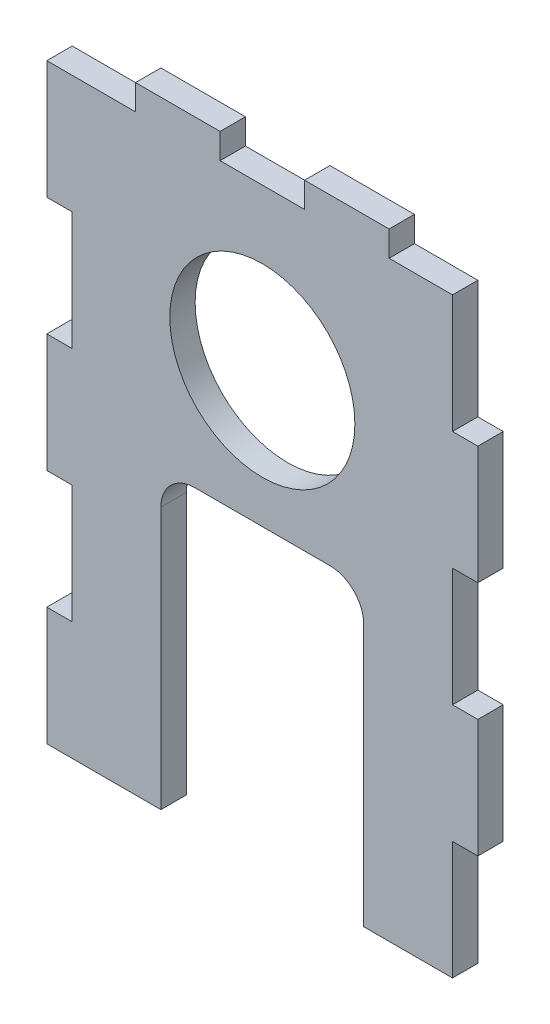
SolidWorks part; units mm, degrees
material "PC High Viscosity"
ref_plane "Front Plane" through (0, 0, 0) normal (0, 0, 1) x (1, 0, 0)
ref_plane "Top Plane" through (0, 0, 0) normal (0, 1, 0) x (1, 0, 0)
ref_plane "Right Plane" through (0, 0, 0) normal (1, 0, 0) x (0, 0, -1)
sketch "Sketch1" plane through (0, 0, 0) normal (0, 0, 1) x (1, 0, 0)
  line L1 (-22.5, -35) -> (22.5, -35)
  line L2 (-22.5, -35) -> (-22.5, 35)
  line L3 (-22.5, 35) -> (22.5, 35)
  line L4 (22.5, -35) -> (22.5, 35)
  line L5 (-22.5, -35) -> (22.5, 35) construction
  line L6 (-22.5, 35) -> (22.5, -35) construction
  point P0 (0, 0)
  dimension "D1" = 70
  dimension "D2" = 45
extrude "Boss-Extrude1" add sketch "Sketch1" along normal blind 3 contours L2 L3 L4 L1
sketch "Sketch2" plane through (0, 0, 3) normal (0, 0, 1) x (1, 0, 0)
  line L0 (-22.5, -35) -> (22.5, -35) construction
  line L1 (-12, 0) -> (12, 0)
  line L2 (-12, 0) -> (-12, -35)
  line L3 (-12, -35) -> (12, -35)
  line L4 (12, 0) -> (12, -35)
  line L5 (-12, 0) -> (12, -35) construction
  line L6 (-12, -35) -> (12, 0) construction
  circle A0 centre (0, 16) radius 10.95
  point P2 (0, -17.5)
  dimension "D1" = 21.9
  dimension "D2" = 16
  dimension "D3" = 24
  dimension "D4" = 35
extrude "Cut-Extrude1" cut sketch "Sketch2" against normal through all
fillet "Fillet1" radius 4 2 edges at (12, 0, 1.5) (-12, 0, 1.5)
sketch "Sketch4" plane through (0, 0, 3) normal (0, 0, 1) x (1, 0, 0)
  line L0 (0, 35) -> (0, 41.52) construction
  line L1 (-15, 35) -> (-5, 35)
  line L2 (-15, 35) -> (-15, 38)
  line L3 (-15, 38) -> (-5, 38)
  line L4 (-5, 35) -> (-5, 38)
  line L5 (-22.5, 35) -> (22.5, 35) construction
  line L6 (5, 35) -> (5, 38)
  line L7 (15, 38) -> (5, 38)
  line L8 (15, 35) -> (15, 38)
  line L9 (15, 35) -> (5, 35)
  dimension "D1" = 3
  dimension "D2" = 10
  dimension "D3" = 10
extrude "Boss-Extrude3" add sketch "Sketch4" against normal up to surface (3 mm away) up to face at (0, -7.6343, 0)
sketch "Sketch3" plane through (0, 0, 0) normal (0, 0, -1) x (-1, 0, 0)
  line L0 (22.5, 7) -> (22.5, -7)
  line L1 (22.5, 35) -> (25.5, 35)
  line L2 (22.5, 35) -> (22.5, 21)
  line L3 (22.5, 21) -> (25.5, 21)
  line L4 (25.5, 35) -> (25.5, 21)
  line L5 (22.5, 7) -> (25.5, 7)
  line L6 (25.5, 7) -> (25.5, -7)
  line L7 (22.5, -7) -> (25.5, -7)
  line L8 (22.5, -21) -> (22.5, -35)
  line L9 (22.5, -21) -> (25.5, -21)
  line L10 (25.5, -21) -> (25.5, -35)
  line L11 (22.5, -35) -> (25.5, -35)
  line L12 (22.5, -35) -> (22.5, 35) construction
  line L13 (-22.5, -35) -> (-22.5, 35) construction
  line L14 (-22.5, 21) -> (-25.5, 21)
  line L15 (-22.5, 21) -> (-22.5, 7)
  line L16 (-22.5, 7) -> (-25.5, 7)
  line L17 (-25.5, 21) -> (-25.5, 7)
  line L18 (22.5, -35) -> (12, -35) construction
  line L19 (-22.5, -7) -> (-25.5, -7)
  line L20 (-22.5, -7) -> (-22.5, -21)
  line L21 (-22.5, -21) -> (-25.5, -21)
  line L22 (-25.5, -7) -> (-25.5, -21)
  dimension "D1" = 3
  dimension "D2" = 14
  dimension "D3" = 3
extrude "Boss-Extrude2" add sketch "Sketch3" against normal up to surface (3 mm away) up to face at (-0.6944, 11.9809, 3)
equation "\"pulley_pitch_diam\"= 12.73mm"
equation "\"pulley_total_width\"= 16mm"
equation "\"belt_width\"= 6mm"
equation "\"material_thickness\"= 3mm"
equation "\"D1@Boss-Extrude1\"=\"material_thickness\""
equation "\"shaft_diam\"= 8mm"
equation "\"D1@Sketch2\"=\"bearing_od\" - 0.1mm"
equation "\"pulley_total_diam\"= 16mm"
equation "\"D2@Sketch2\"=\"pulley_total_diam\" "
equation "\"D3@Sketch2\"=\"pulley_total_width\" * 1.5"
equation "\"D1@Sketch3\"=\"material_thickness\""
equation "\"bearing_od\"= 22mm"
equation "\"bearing_thickness\"= 7mm"
equation "\"D1@Sketch4\"=\"material_thickness\""
